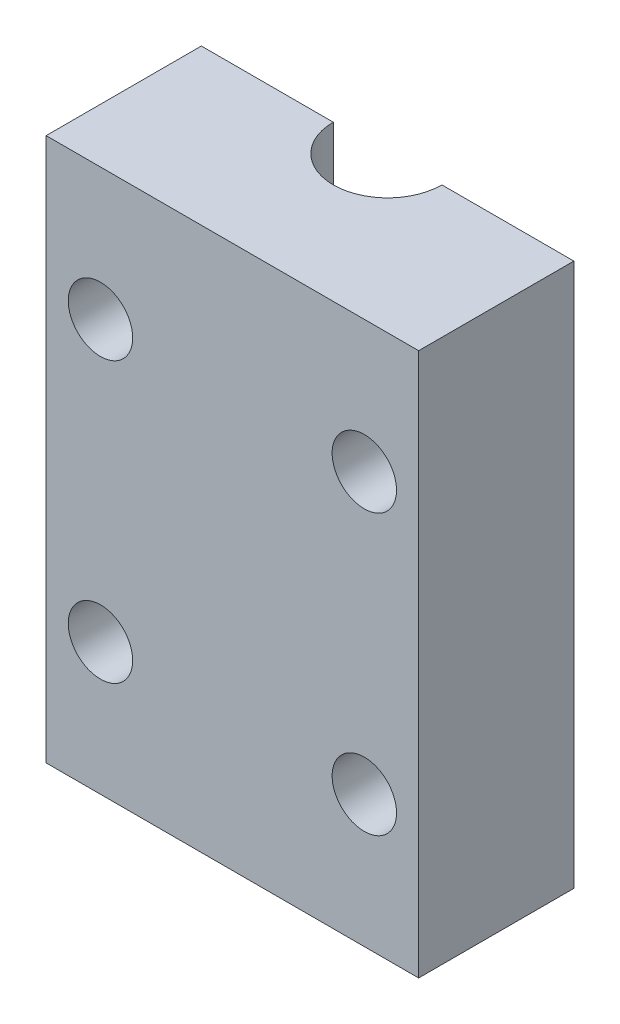
SolidWorks part; units mm, degrees
ref_plane "Спереди" through (0, 0, 0) normal (0, 0, 1) x (1, 0, 0)
ref_plane "Сверху" through (0, 0, 0) normal (0, 1, 0) x (1, 0, 0)
ref_plane "Справа" through (0, 0, 0) normal (1, 0, 0) x (0, 0, -1)
sketch "Sketch1" plane through (0, 0, 0) normal (0, 1, 0) x (1, 0, 0)
  line L1 (24, -10) -> (-24, -10)
  line L2 (24, -10) -> (24, 10)
  line L3 (24, 10) -> (-24, 10)
  line L4 (-24, -10) -> (-24, 10)
  line L5 (24, -10) -> (-24, 10) construction
  line L6 (24, 10) -> (-24, -10) construction
  point P0 (0, 0)
  dimension "D1" = 48
  dimension "D2" = 20
extrude "Boss-Extrude1" add sketch "Sketch1" along normal blind 70
sketch "Sketch2" plane through (24, 0, 0) normal (1, 0, 0) x (0, 0, -1)
  line L0 (-10, 35) -> (10, 35) construction
  line L1 (-10, 70) -> (-10, 0) construction
  line L2 (10, 70) -> (10, 0) construction
  line L3 (3.5, 35) -> (3.5, 70) construction
  line L4 (-1.7, 24.8) -> (8.7, 24.8) construction
  line L5 (-1.7, 24.8) -> (-1.7, 45.2) construction
  line L6 (-1.7, 45.2) -> (8.7, 45.2) construction
  line L7 (8.7, 24.8) -> (8.7, 45.2) construction
  line L8 (-1.7, 24.8) -> (8.7, 45.2) construction
  line L9 (-1.7, 45.2) -> (8.7, 24.8) construction
  line L10 (-10, 70) -> (10, 70) construction
  line L11 (3.5, 35) -> (3.5, 0) construction
  line L12 (-10, 0) -> (10, 0) construction
  line L13 (-5.7606, 42.8) -> (-5.7606, 27.2) construction
  line L14 (8.7, 42.8) -> (-1.7, 42.8)
  line L15 (8.7, 42.8) -> (8.7, 63.2)
  line L16 (8.7, 63.2) -> (-1.7, 63.2)
  line L17 (-1.7, 42.8) -> (-1.7, 63.2)
  line L18 (8.7, 42.8) -> (-1.7, 63.2) construction
  line L19 (8.7, 63.2) -> (-1.7, 42.8) construction
  line L20 (8.7, 6.8) -> (-1.7, 6.8)
  line L21 (8.7, 6.8) -> (8.7, 27.2)
  line L22 (8.7, 27.2) -> (-1.7, 27.2)
  line L23 (-1.7, 6.8) -> (-1.7, 27.2)
  line L24 (8.7, 6.8) -> (-1.7, 27.2) construction
  line L25 (8.7, 27.2) -> (-1.7, 6.8) construction
  line L26 (-1.7, 53) -> (-10, 53) construction
  line L27 (-1.7, 17) -> (-10, 17) construction
  point P6 (3.5, 35)
  point P15 (3.5, 53)
  point P23 (3.5, 17)
  point P30 (-5.7606, 35)
  dimension "D1" = 10.4
  dimension "D2" = 20.4
  dimension "D3" = 13.5
  dimension "D5" = 7.8
sketch "Sketch3" plane through (0, 0, 10) normal (0, 0, 1) x (1, 0, 0)
  line L0 (-24, 35) -> (24, 35) construction
  line L1 (-24, 70) -> (-24, 0) construction
  line L2 (24, 70) -> (24, 0) construction
  line L3 (17, 17) -> (17, 53) construction
  line L4 (-17, 17) -> (-17, 53) construction
  line L5 (24, 53) -> (-24, 53) construction
  line L6 (24, 17) -> (-24, 17) construction
  circle A0 centre (-17, 35) radius 4.15 construction
  circle A1 centre (17, 35) radius 4.15 construction
  circle A2 centre (17, 53) radius 4.15
  circle A3 centre (-17, 53) radius 4.15
  circle A4 centre (-17, 17) radius 4.15
  circle A5 centre (17, 17) radius 4.15
  point P10 (0, 35)
  point P13 (17, 35)
  point P17 (-17, 35)
  dimension "D1" = 34
  dimension "D2" = 8.3
  dimension "D3" = 17
extrude "Cut-Extrude2" cut sketch "Sketch3" against normal through all
sketch "Sketch4" plane through (0, 70, 0) normal (0, 1, 0) x (1, 0, 0)
  line L0 (0, 10) -> (0, -10) construction
  line L1 (24, 10) -> (-24, 10) construction
  line L2 (-24, -10) -> (24, -10) construction
  arc A0 (-7, 10) -> (7, 10) centre (0, 10) ccw
  dimension "D1" = 7
extrude "Cut-Extrude3" cut sketch "Sketch4" against normal through all and the other way through all
